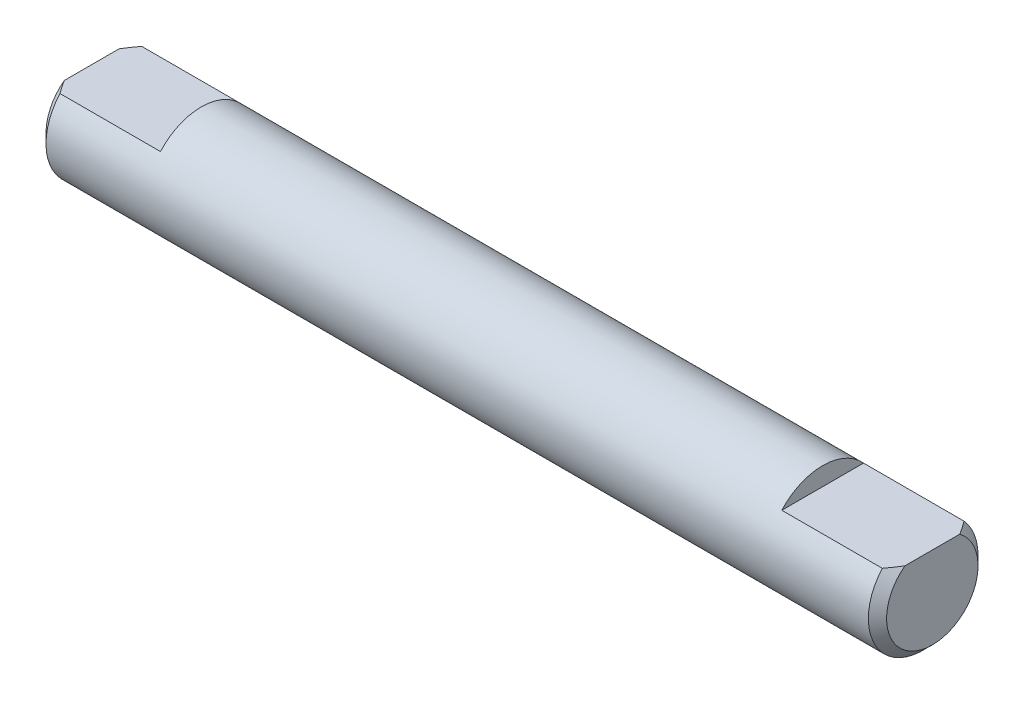
SolidWorks part; units mm, degrees
ref_plane "Front Plane" through (0, 0, 0) normal (0, 0, 1) x (1, 0, 0)
ref_plane "Top Plane" through (0, 0, 0) normal (0, 1, 0) x (1, 0, 0)
ref_plane "Right Plane" through (0, 0, 0) normal (1, 0, 0) x (0, 0, -1)
sketch "Sketch2" plane through (0, 0, 0) normal (0, 0, 1) x (1, 0, 0)
  line L0 (0, 0) -> (46, 0)
  line L1 (46, 0) -> (46, -3)
  line L2 (46, -3) -> (0, -3)
  line L3 (0, -3) -> (0, 0)
  dimension "D1" = 46
  dimension "D2" = 3
revolve "Revolve2" add sketch "Sketch2" angle 360 about L0
sketch "Sketch7" plane through (46, 0, 0) normal (1, 0, 0) x (0, 0, -1)
  line L0 (-2.2361, 2) -> (2.2361, 2)
  circle A1 centre (0, 0) radius 3
  arc A2 (2.2361, 2) -> (-2.2361, 2) centre (0, 0) ccw
  dimension "D2" = 2
  dimension "D1" = 0
extrude "Cut-Extrude3" cut sketch "Sketch7" against normal blind 6
sketch "Sketch8" plane through (0, 0, 0) normal (-1, 0, 0) x (0, 0, 1)
  line L0 (-2.2361, 2) -> (2.2361, 2)
  circle A1 centre (0, 0) radius 3
  arc A2 (2.2361, 2) -> (-2.2361, 2) centre (0, 0) ccw
  dimension "D2" = 2
  dimension "D1" = 0
extrude "Cut-Extrude4" cut sketch "Sketch8" against normal blind 6
chamfer "Chamfer2" distance 0.5 angle 45 2 edges at (46, -3, 0) (0, -3, 0)
